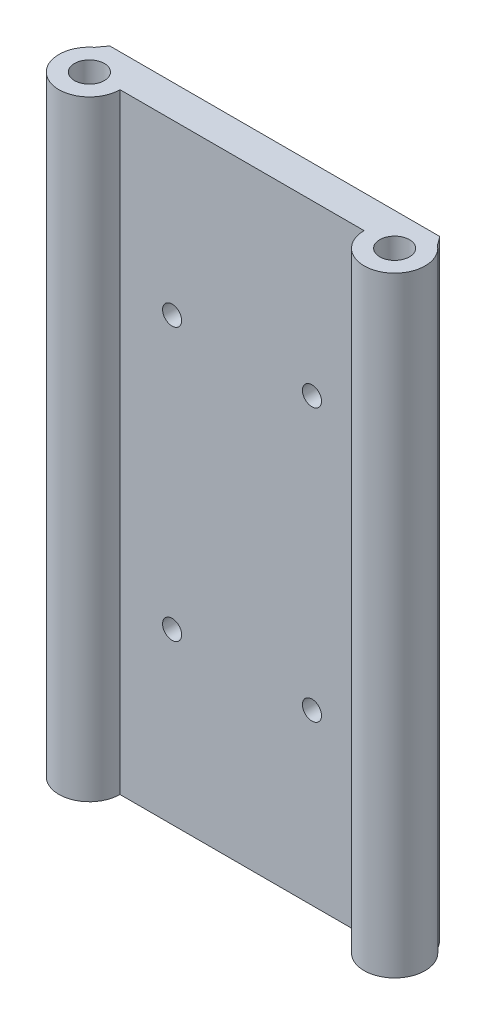
SolidWorks part; units mm, degrees
material "ABS"
ref_plane "Front Plane" through (0, 0, 0) normal (0, 0, 1) x (1, 0, 0)
ref_plane "Top Plane" through (0, 0, 0) normal (0, 1, 0) x (1, 0, 0)
ref_plane "Right Plane" through (0, 0, 0) normal (1, 0, 0) x (0, 0, -1)
sketch "Sketch1" plane through (0, 0, 0) normal (0, 1, 0) x (1, 0, 0)
  line L0 (-50.8, 0) -> (50.8, 0) construction
  line L1 (-40.64, 0) -> (40.64, 0)
  line L2 (-54.8982, 10.9145) -> (54.8982, 10.9145)
  circle A0 centre (-50.8, 0) radius 4.9609
  circle A1 centre (50.8, 0) radius 4.9609
  circle A2 centre (-50.8, 0) radius 10.16
  circle A4 centre (50.8, 0) radius 10.16
  arc A5 (57.0241, 8.0303) -> (-57.0241, 8.0303) centre (0, -31.7761) ccw
  point P4 (0, 0)
  dimension "D1" = 9.9219
  dimension "D2" = 101.6
  dimension "D3" = 20.32
extrude "Boss-Extrude1" add sketch "Sketch1" along normal mid plane 203.2
sketch "Sketch2" plane through (0, 0, 0) normal (0, 0, 1) x (1, 0, 0)
  line L0 (-23.2789, 0) -> (23.2789, 0) construction
  line L1 (-23.2789, -45.2995) -> (23.2789, -45.2995) construction
  line L2 (-23.2789, -45.2995) -> (-23.2789, 45.2995) construction
  line L3 (-23.2789, 45.2995) -> (23.2789, 45.2995) construction
  line L4 (23.2789, -45.2995) -> (23.2789, 45.2995) construction
  line L5 (-23.2789, -45.2995) -> (23.2789, 45.2995) construction
  line L6 (-23.2789, 45.2995) -> (23.2789, -45.2995) construction
  circle A0 centre (-23.2789, 45.2995) radius 3.175
  circle A1 centre (23.2789, 45.2995) radius 3.175
  circle A2 centre (23.2789, -45.2995) radius 3.175
  circle A3 centre (-23.2789, -45.2995) radius 3.175
  point P0 (0, 0)
  dimension "D1" = 6.35
extrude "Cut-Extrude1" cut sketch "Sketch2" against normal through all both and the other way through all
sketch "Sketch3" plane through (0, 0, 0) normal (0, 0, 1) x (1, 0, 0)
  line L0 (-34.5268, 0) -> (34.5268, 0)
  line L1 (-34.5268, -64.8934) -> (34.5268, -64.8934)
  line L2 (-34.5268, -64.8934) -> (-34.5268, 64.8934)
  line L3 (-34.5268, 64.8934) -> (34.5268, 64.8934)
  line L4 (34.5268, -64.8934) -> (34.5268, 64.8934)
  line L5 (-34.5268, -64.8934) -> (34.5268, 64.8934) construction
  line L6 (-34.5268, 64.8934) -> (34.5268, -64.8934) construction
  circle A0 centre (-34.5268, 64.8934) radius 5.5562
  circle A1 centre (34.5268, 64.8934) radius 5.5562
  circle A2 centre (34.5268, -64.8934) radius 5.5562
  circle A3 centre (-34.5268, -64.8934) radius 5.5563
  point P0 (0, 0)
  dimension "D1" = 11.1125
